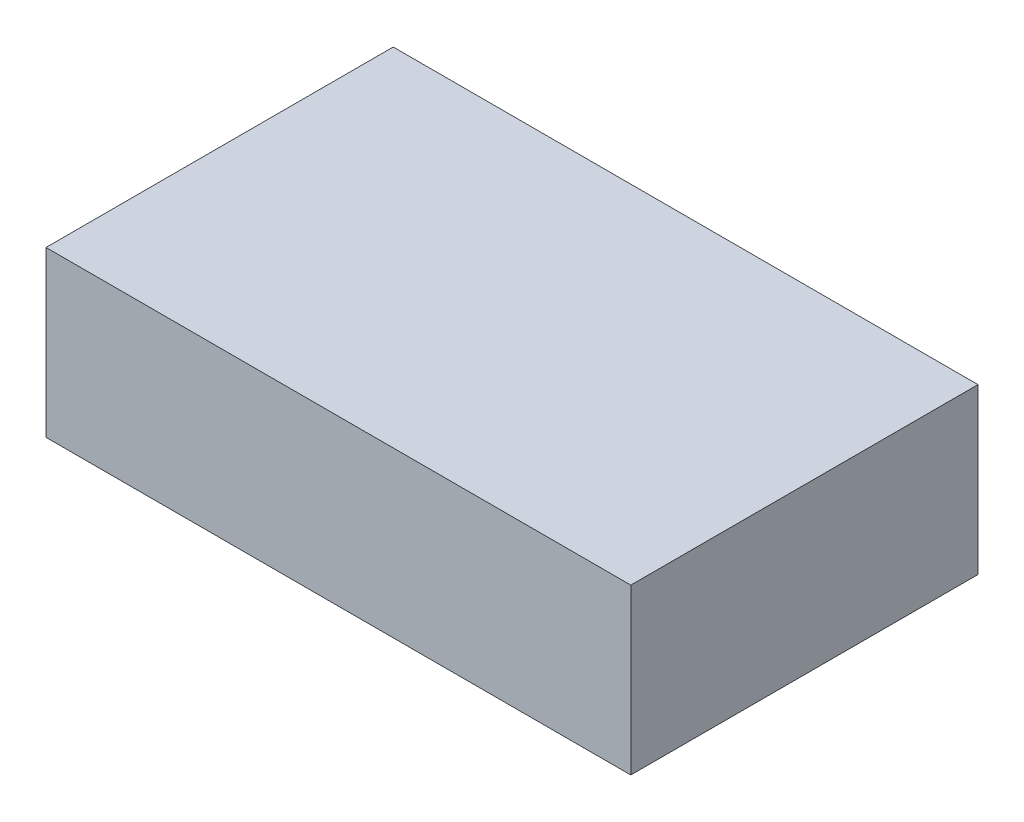
SolidWorks part; units mm, degrees
ref_plane "Front Plane" through (0, 0, 0) normal (0, 0, 1) x (1, 0, 0)
ref_plane "Top Plane" through (0, 0, 0) normal (0, 1, 0) x (1, 0, 0)
ref_plane "Right Plane" through (0, 0, 0) normal (1, 0, 0) x (0, 0, -1)
sketch "Sketch1" plane through (0, 0, 0) normal (0, 1, 0) x (1, 0, 0)
  line L1 (-16, -9.5) -> (16, -9.5)
  line L2 (-16, -9.5) -> (-16, 9.5)
  line L3 (-16, 9.5) -> (16, 9.5)
  line L4 (16, -9.5) -> (16, 9.5)
  line L5 (-16, -9.5) -> (16, 9.5) construction
  line L6 (-16, 9.5) -> (16, -9.5) construction
  point P0 (0, 0)
  dimension "D1" = 32
  dimension "D2" = 19
extrude "Boss-Extrude1" add sketch "Sketch1" along normal blind 9
